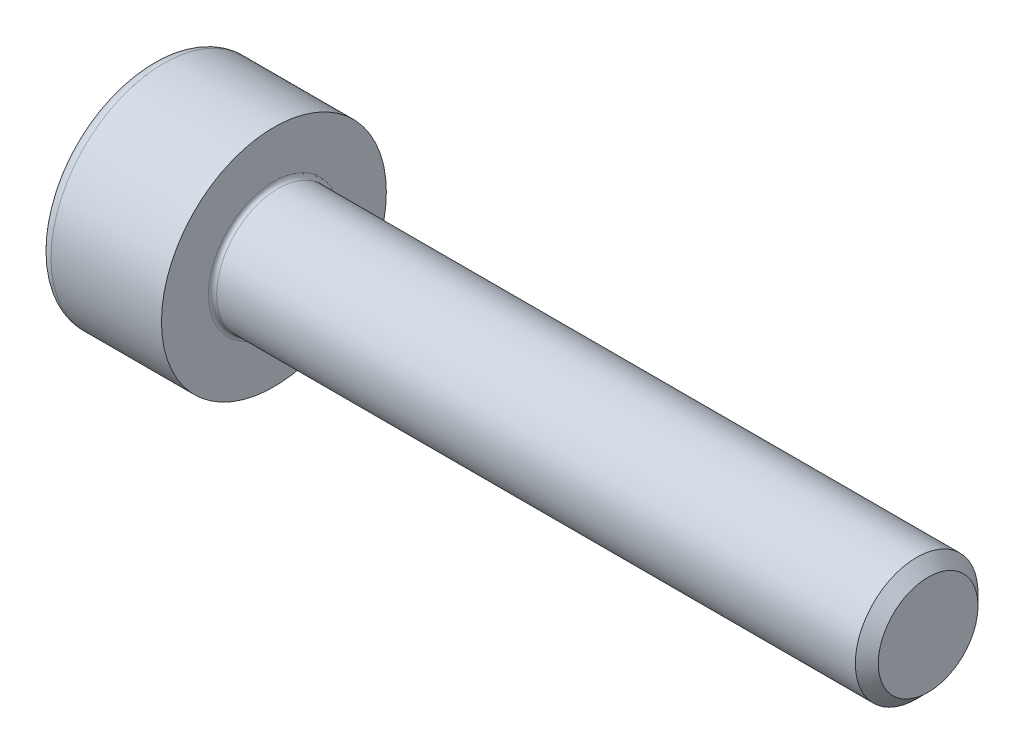
SolidWorks part; units mm, degrees
revolve "Base-Revolve" add sketch "BodySke"
sketch "BodySke" plane through (0, 0, 0) normal (0, 0, 1) x (1, 0, 0)
  line L0 (0, 0) -> (0, 2.75)
  line L1 (0, 2.75) -> (3, 2.75)
  line L2 (3, 2.75) -> (3, 1.5)
  line L3 (3, 1.5) -> (18.7195, 1.5)
  line L4 (19, 1.2195) -> (19, 0)
  line L5 (19, 0) -> (0, 0)
  line L6 (-31.75, 0) -> (127, 0) construction
  line L8 (19, 1.2195) -> (18.7195, 1.5)
  line L10 (19, -1.2195) -> (18.7195, -1.5) construction
  line L11 (3.5, 9.525) -> (3.5, 3.175) construction
  line L12 (14, 9.525) -> (14, 3.175) construction
  line L13 (-41, 9.525) -> (-41, 3.175) construction
  dimension "Head_ht" = 3
  dimension "Length" = 16
  dimension "Body_ch_ang" = 45
  dimension "Diameter" = 3
  dimension "Minor_dia" = 2.439
  dimension "Advance" = 0.5
  dimension "Thread_nom" = 5
  dimension "Thread_length" = 60
  dimension "Head_dia" = 5.5
cosmetic thread "ThreadCosmetic" [suppressed]
fillet "Fillet1" radius 0.1 1 edges at (3, 0, 1.5)
fillet "Fillet2" radius 0.3 1 edges at (0, 0, 2.75)
ref_plane "Plane1" through (0, 0, 0) normal (0, 0, 1) x (1, 0, 0)
ref_plane "Plane2" through (0, 0, 0) normal (0, 1, 0) x (1, 0, 0)
ref_plane "Plane3" through (0, 0, 0) normal (1, 0, 0) x (0, 0, -1)
other "Configuration Table"
sketch "Sketch2" plane through (0, 0, 0) normal (0, 0, 1) x (1, 0, 0)
  line L0 (0, 1.26) -> (1.3, 1.26)
  line L1 (1.3, 1.26) -> (2.0275, 0)
  line L2 (-31.75, 0) -> (127, 0) construction
  line L3 (2.0275, 0) -> (0, 0)
  line L4 (0, 0) -> (0, 1.26)
  line L6 (0, 0) -> (47.625, 0) construction
  dimension "D1" = 1.26
  dimension "D2" = 60
  dimension "Depth" = 1.3
revolve "Hex-PreBroach" cut sketch "Sketch2" angle 360 about L6
sketch "Sketch3" plane through (0, 0, 0) normal (-1, 0, 0) x (0, 0.5, 0.866)
  line L0 (0.7275, 1.26) -> (-0.7275, 1.26)
  line L1 (-0.7275, 1.26) -> (-1.4549, 0)
  line L2 (0.7275, 1.26) -> (1.4549, 0)
  line L3 (0.7275, -1.26) -> (1.4549, 0)
  line L4 (0.7275, -1.26) -> (-0.7275, -1.26)
  line L5 (-0.7275, -1.26) -> (-1.4549, 0)
  dimension "D1" = 1.26
  dimension "D2" = 1.26
  dimension "Hex_size" = 2.52
extrude "Hex" cut sketch "Sketch3" against normal blind 1.3
sketch "ThdSchSke" plane through (0, 0, 0) normal (0, 0, 1) x (1, 0, 0)
  line L0 (14, -1.2195) -> (13.8036, -1.5)
  line L1 (14, -1.2195) -> (14.1964, -1.5)
  line L2 (14.1964, -1.5) -> (14.1964, -1.875)
  line L3 (-3.175, 0) -> (5.1513, 0) construction
  line L4 (0, 2.45) -> (0, -2.45) construction
  line L5 (14.1964, -1.875) -> (13.8036, -1.875)
  line L6 (13.8036, -1.875) -> (13.8036, -1.5)
  dimension "Thread_minor" = 2.439
  dimension "Diameter" = 3
  dimension "Start" = 14
revolve "ThreadSchematic" [suppressed] cut sketch "ThdSchSke" angle 360 about L3
pattern_linear "ThdSchPat" [suppressed]
equation "\"D2@Sketch3\" = \"Hex_size@Sketch3\" / 2"
equation "\"D1@Sketch3\" = \"Hex_size@Sketch3\" / 2"
equation "\"D1@Sketch2\" = \"Hex_size@Sketch3\" / 2"
equation "\"Thread_minor@ThreadCosmetic\"  =  \"Minor_dia@BodySke\""
equation "\"Depth@Sketch2\" =  \"Key_eng@Hex\""
equation "\"Thread_length@ThreadCosmetic\" = ((sgn( (\"Length@BodySke\" - \"Advance@BodySke\" * 3.0) - \"Thread_nom@BodySke\" )-1)*( (\"Length@BodySke\" - \"Advance@BodySke\" * 3.0) - \"Thread_nom@BodySke\" ))/-2+ \"Thread_nom@BodySke\""
equation "\"Thread_minor@ThdSchSke\" = \"Minor_dia@BodySke\""
equation "\"Diameter@ThdSchSke\" = \"Diameter@BodySke\""
equation "\"Overcut@ThdSchSke\" = \"Diameter@BodySke\" * 1.25"
equation "\"Start@ThdSchSke\" = \"Head_ht@BodySke\" + \"Length@BodySke\" - \"Thread_length@ThreadCosmetic\"  '---Non-countersunk---"
equation "\"Num_threads@ThdSchPat\" = int( \"Thread_length@ThreadCosmetic\" / \"Advance@BodySke\" + 0.999 )  + 1"
equation "\"Advance@ThdSchPat\" = \"Thread_length@ThreadCosmetic\" /  (\"Num_threads@ThdSchPat\" - 1) 'relax it"
equation "\"Num_threads@ThdSchPat\" = \"Num_threads@ThdSchPat\" - sgn( \"Num_threads@ThdSchPat\" - 1) '---chamfered tips only---"
